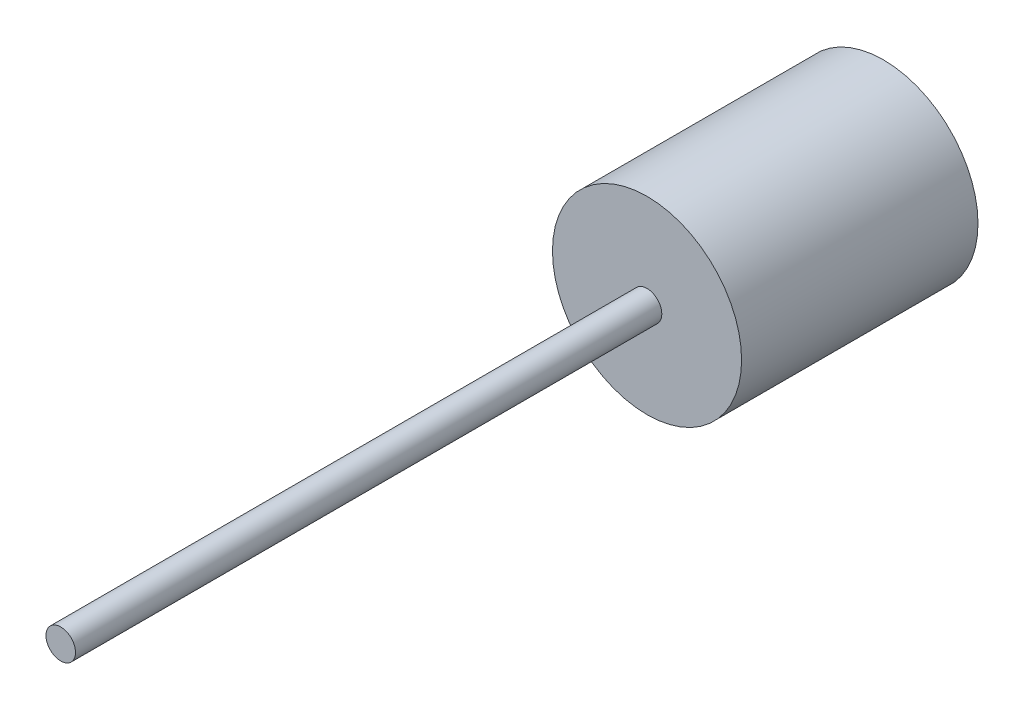
SolidWorks part; units mm, degrees
ref_plane "Front Plane" through (0, 0, 0) normal (0, 0, 1) x (1, 0, 0)
ref_plane "Top Plane" through (0, 0, 0) normal (0, 1, 0) x (1, 0, 0)
ref_plane "Right Plane" through (0, 0, 0) normal (1, 0, 0) x (0, 0, -1)
sketch "Sketch1" plane through (0, 0, 0) normal (0, 0, 1) x (1, 0, 0)
  circle A0 centre (0, 0) radius 12.7
  dimension "D1" = 25.4
extrude "Boss-Extrude1" add sketch "Sketch1" along normal blind 31.75 contours A0
sketch "Sketch2" plane through (0, 0, 31.75) normal (0, 0, 1) x (1, 0, 0)
  circle A0 centre (0, 0) radius 1.9844
  dimension "D1" = 3.9688
extrude "Boss-Extrude2" add sketch "Sketch2" along normal blind 78.74
